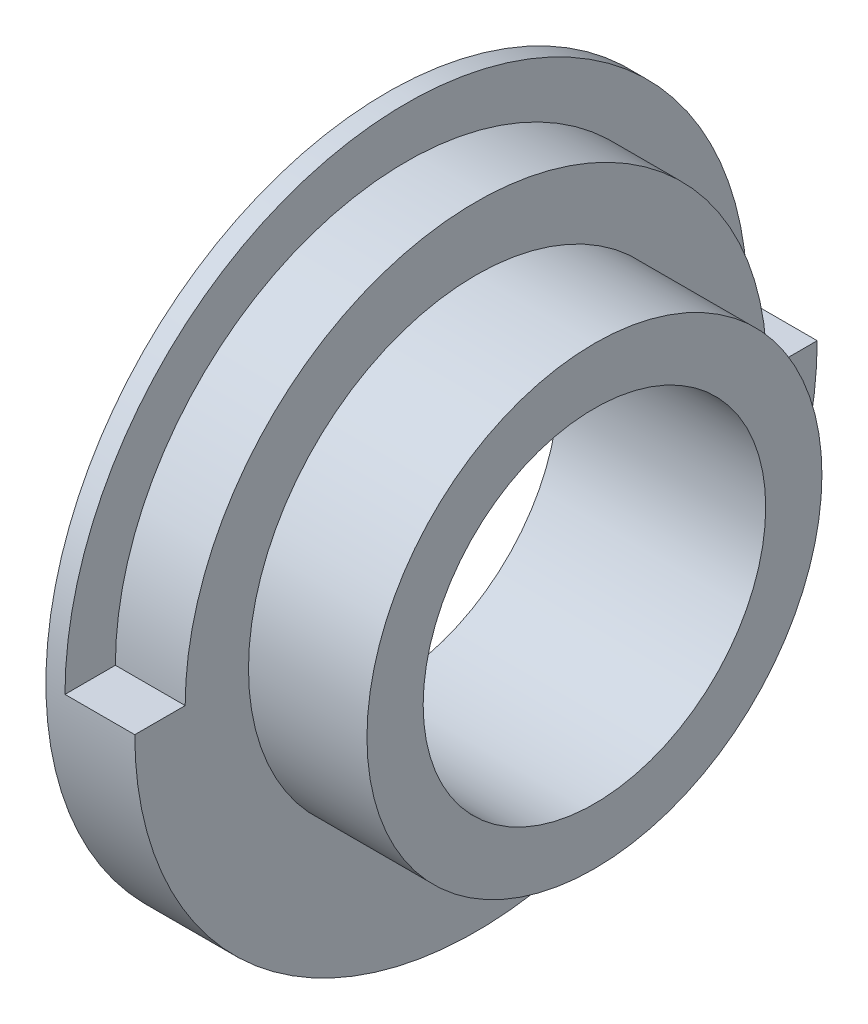
SolidWorks part; units mm, degrees
ref_plane "Ön Düzlem" through (0, 0, 0) normal (0, 0, 1) x (1, 0, 0)
ref_plane "Üst Düzlem" through (0, 0, 0) normal (0, 1, 0) x (1, 0, 0)
ref_plane "Sağ Düzlem" through (0, 0, 0) normal (1, 0, 0) x (0, 0, -1)
sketch "Çizim1" plane through (0, 0, 0) normal (0, 0, 1) x (1, 0, 0)
  line L0 (0, 0) -> (-57.4025, 0) construction
  line L1 (0, 29.1959) -> (-35.3431, 29.1959)
  line L2 (0, 29.1959) -> (0, 38.7773)
  line L3 (-20.1912, 58.1628) -> (-35.3431, 58.1628)
  line L4 (-35.3431, 29.1959) -> (-35.3431, 58.1628)
  line L6 (-20.1912, 58.1628) -> (-20.1912, 38.7773)
  line L7 (-20.1912, 38.7773) -> (0, 38.7773)
revolve "Döndür1" add sketch "Çizim1" angle 360 about L0
sketch "Çizim2" plane through (0, 0, 0) normal (0, 0, 1) x (1, 0, 0)
  line L0 (0, 0) -> (-69.971, 0) construction
  line L1 (-32.0893, 66.5764) -> (-7.9377, 66.5764)
  line L2 (-32.0893, 66.5764) -> (-32.0893, 49.5702)
  line L3 (-32.0893, 49.5702) -> (-7.9377, 49.5702)
  line L4 (-7.9377, 66.5764) -> (-7.9377, 49.5702)
revolve "Kes-Döndür1" cut sketch "Çizim2" angle 180 mid plane about L0
